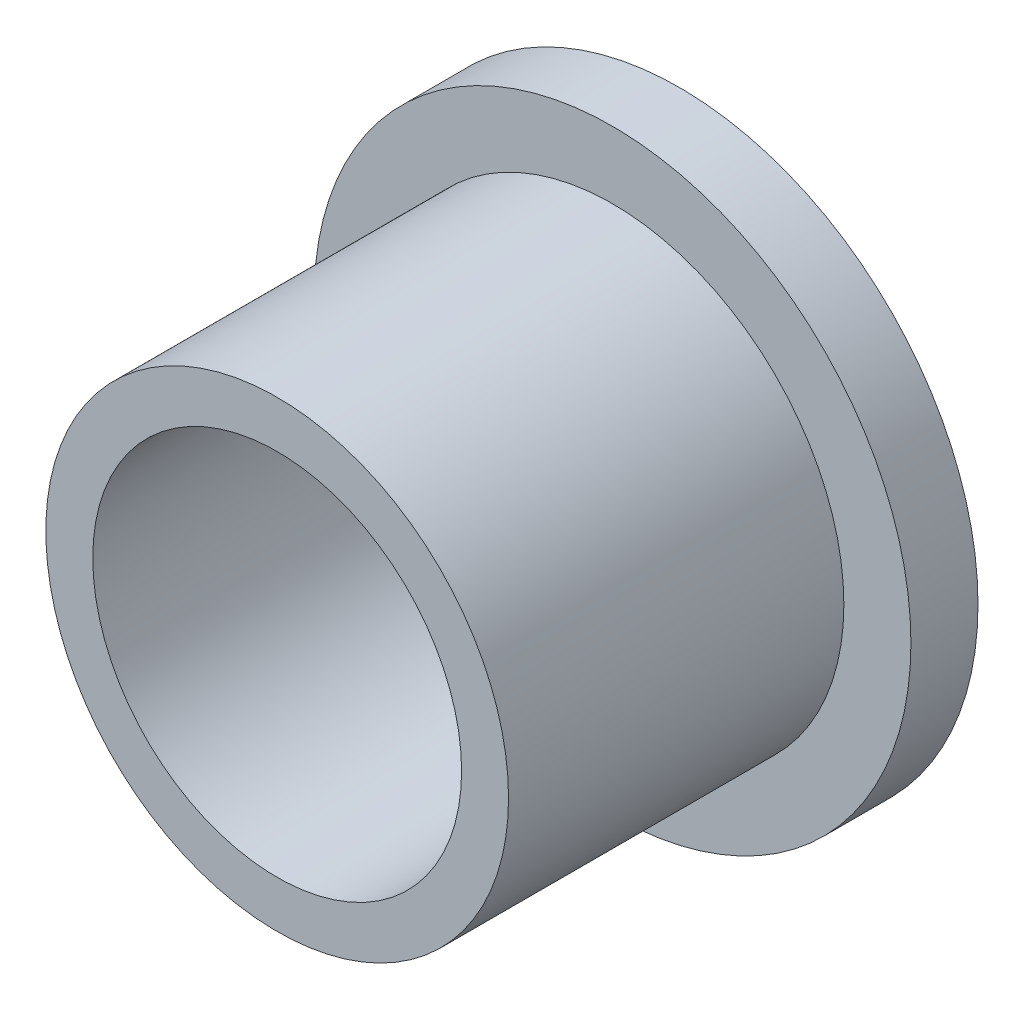
SolidWorks part; units mm, degrees
ref_plane "Front Plane" through (0, 0, 0) normal (0, 0, 1) x (1, 0, 0)
ref_plane "Top Plane" through (0, 0, 0) normal (0, 1, 0) x (1, 0, 0)
ref_plane "Right Plane" through (0, 0, 0) normal (1, 0, 0) x (0, 0, -1)
sketch "Croquis1" plane through (0, 0, 0) normal (1, 0, 0) x (0, 0, -1)
  line L0 (-10.3909, 3.45) -> (-10.3909, -3.45)
  line L1 (-10.3909, 3.45) -> (-5.3909, 3.45)
  line L2 (-5.3909, 3.45) -> (-5.3909, 4.45)
  line L3 (-5.3909, 4.45) -> (-4.3909, 4.45)
  line L4 (-4.3909, 4.45) -> (-4.3909, -4.45)
  line L5 (-4.3909, -4.45) -> (-5.3909, -4.45)
  line L6 (-5.3909, -4.45) -> (-5.3909, -3.45)
  line L7 (-5.3909, -3.45) -> (-10.3909, -3.45)
  line L8 (-12.0727, 0) -> (18.863, 0) construction
  point P2 (-10.3909, 0)
  dimension "D1" = 6.9
  dimension "D2" = 1
  dimension "D3" = 1
  dimension "D4" = 5
  dimension "D5" = 1
  dimension "D6" = 4.3909
revolve "Revolución1" add sketch "Croquis1" angle 360 about L8
sketch "Croquis2" plane through (0, 0, 10.3909) normal (0, 0, 1) x (1, 0, 0)
  circle A0 centre (0, 0) radius 2.75
  dimension "D1" = 5.5
extrude "Cortar-Extruir1" cut sketch "Croquis2" against normal blind 10
